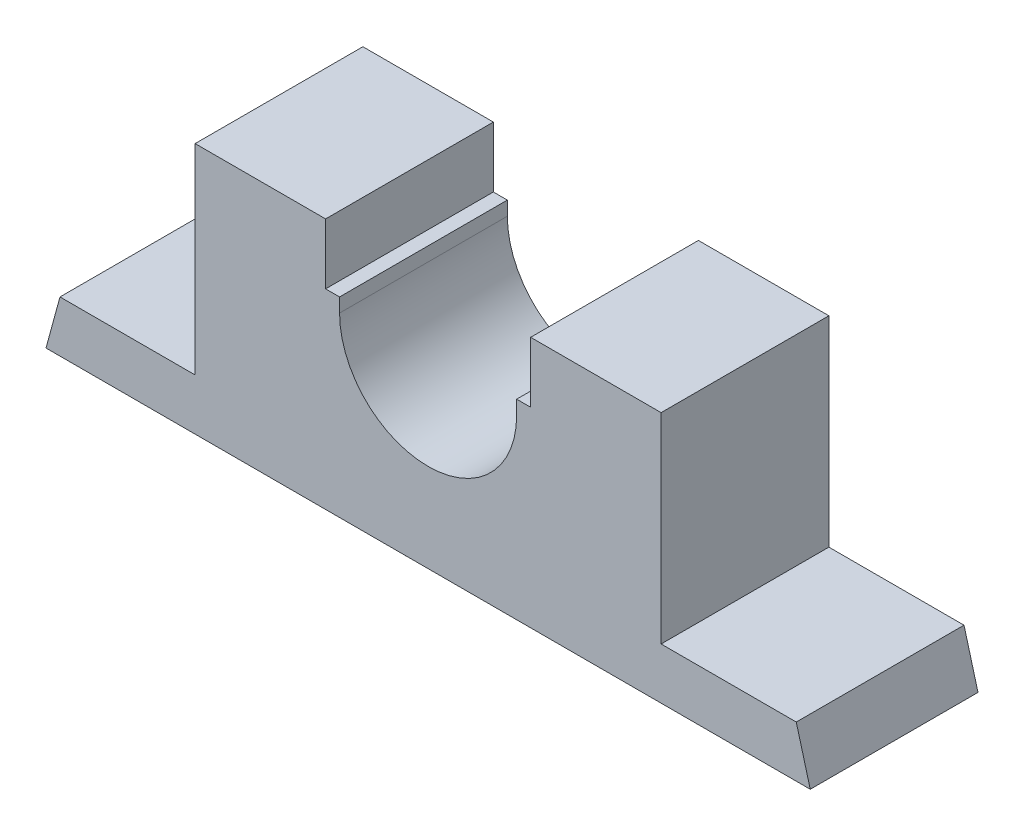
SolidWorks part; units mm, degrees
ref_plane "Front Plane" through (0, 0, 0) normal (0, 0, 1) x (1, 0, 0)
ref_plane "Top Plane" through (0, 0, 0) normal (0, 1, 0) x (1, 0, 0)
ref_plane "Right Plane" through (0, 0, 0) normal (1, 0, 0) x (0, 0, -1)
sketch "Sketch1" plane through (0, 0, 0) normal (0, 0, 1) x (1, 0, 0)
  line L0 (-82, 0) -> (82, 0)
  line L1 (-79, 11) -> (-82, 0)
  line L2 (79, 11) -> (50, 11)
  line L3 (50, 11) -> (50, 54)
  line L4 (50, 54) -> (22, 54)
  line L5 (22, 54) -> (22, 41)
  line L6 (22, 41) -> (19, 41)
  line L7 (19, 41) -> (19, 38)
  line L8 (0, 0) -> (0, 89.5013) construction
  line L9 (79, 11) -> (82, 0)
  line L10 (-79, 11) -> (-50, 11)
  line L11 (-50, 11) -> (-50, 54)
  line L12 (-50, 54) -> (-22, 54)
  line L13 (-22, 54) -> (-22, 41)
  line L14 (-22, 41) -> (-19, 41)
  line L15 (-19, 41) -> (-19, 38)
  arc A0 (-19, 38) -> (19, 38) centre (0, 38) ccw
  point P12 (79, 11)
  dimension "D1" = 82
  dimension "D2" = 50
  dimension "D3" = 3
  dimension "D4" = 3
  dimension "D5" = 13
  dimension "D6" = 19
  dimension "D7" = 54
  dimension "D8" = 11
extrude "Boss-Extrude2" add sketch "Sketch1" along normal blind 36
